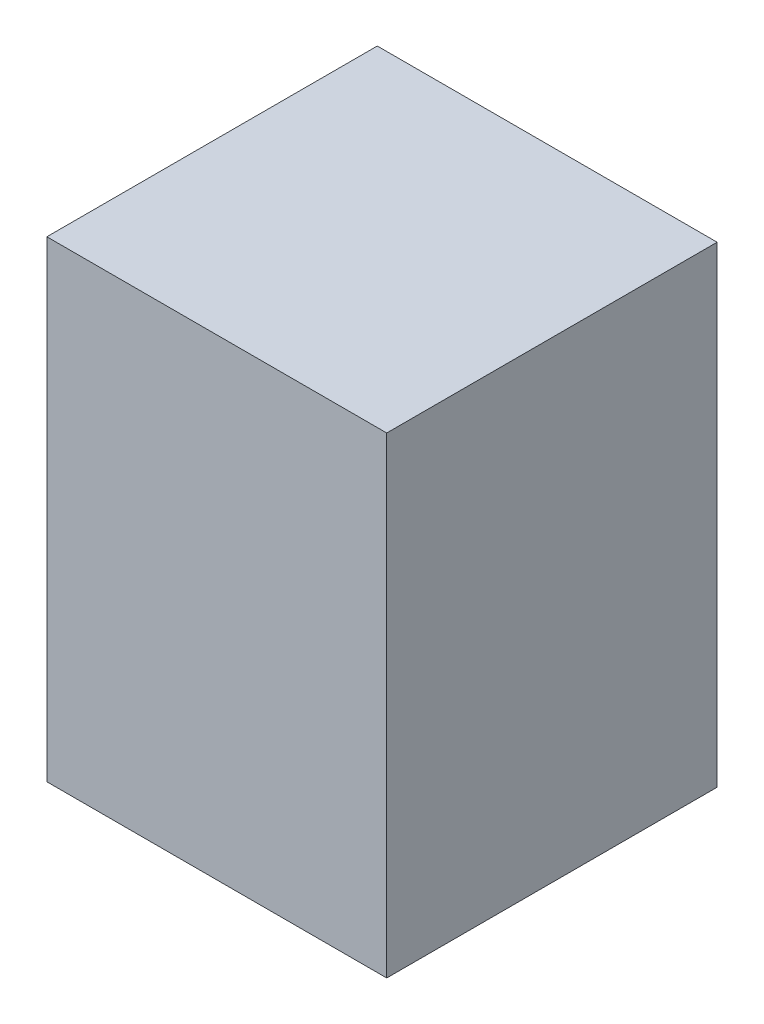
SolidWorks part; units mm, degrees
ref_plane "Спереди" through (0, 0, 0) normal (0, 0, 1) x (1, 0, 0)
ref_plane "Сверху" through (0, 0, 0) normal (0, 1, 0) x (1, 0, 0)
ref_plane "Справа" through (0, 0, 0) normal (1, 0, 0) x (0, 0, -1)
sketch "Эскиз1" plane through (0, 0, 0) normal (0, 0, 1) x (1, 0, 0)
  line L0 (0, 0) -> (72, 0)
  line L1 (0, 0) -> (0, 100)
  line L2 (72, 0) -> (72, 100)
  line L3 (0, 100) -> (72, 100)
  dimension "D1" = 72
  dimension "D2" = 100
extrude "Бобышка-Вытянуть1" add sketch "Эскиз1" along normal blind 70
sketch "Эскиз2" plane through (0, 0, 0) normal (0, -1, 0) x (1, 0, 0)
  line L0 (40, 70) -> (40, 0) construction
  line L1 (0, 70) -> (72, 70) construction
  line L2 (0, 0) -> (72, 0) construction
  line L3 (0, 70) -> (0, 0) construction
  circle A0 centre (40, 50) radius 2
  circle A1 centre (40, 20) radius 2
  dimension "D2" = 4
  dimension "D3" = 4
  dimension "D4" = 20
  dimension "D5" = 20
  dimension "D1" = 40
extrude "Вырез-Вытянуть1" cut sketch "Эскиз2" against normal blind 10
ref_plane "Отверстия" through (40, 0, 0) normal (-1, 0, 0) x (0, 0, -1)
